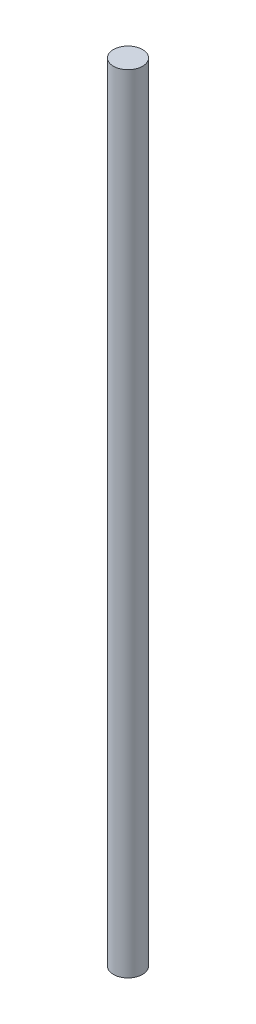
SolidWorks part; units mm, degrees
ref_plane "Front Plane" through (0, 0, 0) normal (0, 0, 1) x (1, 0, 0)
ref_plane "Top Plane" through (0, 0, 0) normal (0, 1, 0) x (1, 0, 0)
ref_plane "Right Plane" through (0, 0, 0) normal (1, 0, 0) x (0, 0, -1)
sketch "Sketch2" plane through (0, 0, 0) normal (0, 1, 0) x (1, 0, 0)
  circle A0 centre (0, 0) radius 4.7625
  dimension "D1" = 9.525
extrude "Boss-Extrude1" add sketch "Sketch2" along normal blind 257.81
